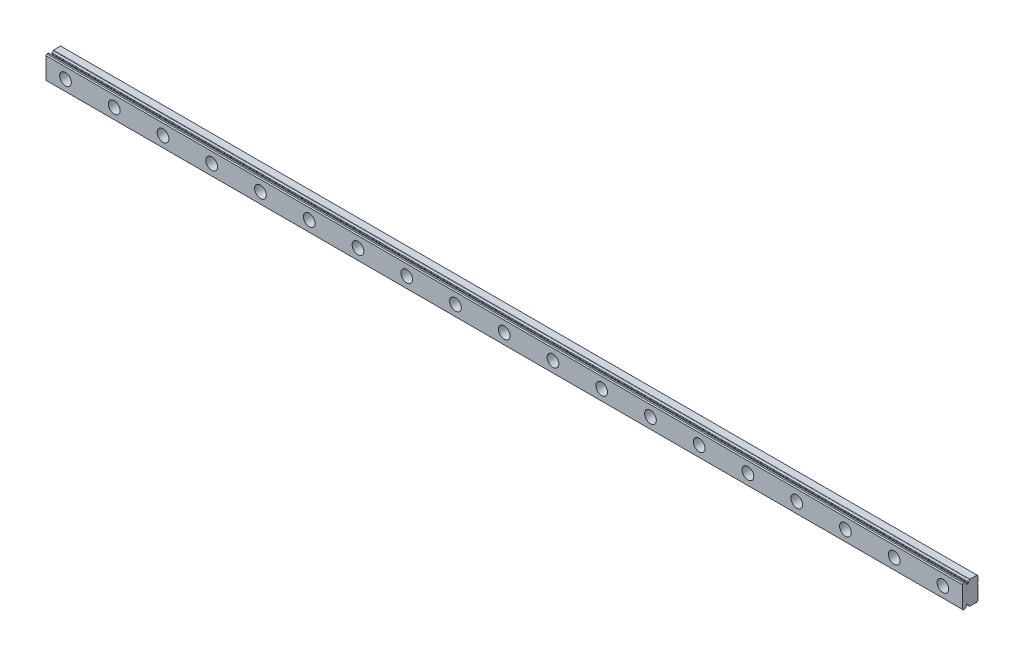
SolidWorks part; units mm, degrees
ref_plane "Front" through (0, 0, 0) normal (0, 0, 1) x (1, 0, 0)
ref_plane "Top" through (0, 0, 0) normal (0, 1, 0) x (1, 0, 0)
ref_plane "Right" through (0, 0, 0) normal (1, 0, 0) x (0, 0, -1)
ref_plane "Plane1" through (-10, 0, 0) normal (-1, 0, 0) x (0, -1, 0)
sketch "Sketch1" plane through (-10, 0, 0) normal (-1, 0, 0) x (0, -1, 0)
  line L0 (5.5, 0) -> (6, 0.5)
  line L1 (6, 0.5) -> (6, 4.1421)
  line L2 (5.0738, 4.9945) -> (4.7282, 5.0247)
  line L3 (4.5, 5.2738) -> (4.5, 5.7262)
  line L4 (4.7282, 5.9753) -> (5.0948, 6.0073)
  line L5 (6, 6.8254) -> (6, 7.5)
  line L6 (6, 7.5) -> (5.5, 8)
  line L7 (5.5, 8) -> (-5.5, 8)
  line L8 (-5.5, 8) -> (-6, 7.5)
  line L9 (-6, 7.5) -> (-6, 6.8254)
  line L10 (-5.0948, 6.0073) -> (-4.7282, 5.9753)
  line L11 (-4.5, 5.7262) -> (-4.5, 5.2738)
  line L12 (-4.7282, 5.0247) -> (-5.0738, 4.9945)
  line L13 (-6, 4.1421) -> (-6, 0.5)
  line L14 (-6, 0.5) -> (-5.5, 0)
  line L15 (-5.5, 0) -> (-2.4, 0)
  line L16 (-1.6, 0) -> (5.5, 0)
  arc A0 (6, 4.1421) -> (5.8448, 4.3734) centre (5.75, 4.1421) ccw
  arc A1 (5.8448, 4.3734) -> (5.2672, 4.8727) centre (6.3, 5.4838) cw
  arc A2 (5.2672, 4.8727) -> (5.0738, 4.9945) centre (5.052, 4.7455) ccw
  arc A3 (4.7282, 5.0247) -> (4.5, 5.2738) centre (4.75, 5.2738) cw
  arc A4 (4.5, 5.7262) -> (4.7282, 5.9753) centre (4.75, 5.7262) cw
  arc A5 (5.0948, 6.0073) -> (5.2845, 6.1232) centre (5.073, 6.2564) ccw
  arc A6 (5.2845, 6.1232) -> (5.8448, 6.5941) centre (6.3, 5.4838) cw
  arc A7 (5.8448, 6.5941) -> (6, 6.8254) centre (5.75, 6.8254) ccw
  arc A8 (-6, 6.8254) -> (-5.8448, 6.5941) centre (-5.75, 6.8254) ccw
  arc A9 (-5.8448, 6.5941) -> (-5.2845, 6.1232) centre (-6.3, 5.4838) cw
  arc A10 (-5.2845, 6.1232) -> (-5.0948, 6.0073) centre (-5.073, 6.2564) ccw
  arc A11 (-4.7282, 5.9753) -> (-4.5, 5.7262) centre (-4.75, 5.7262) cw
  arc A12 (-4.5, 5.2738) -> (-4.7282, 5.0247) centre (-4.75, 5.2738) cw
  arc A13 (-5.0738, 4.9945) -> (-5.2672, 4.8727) centre (-5.052, 4.7455) ccw
  arc A14 (-5.2672, 4.8727) -> (-5.8448, 4.3734) centre (-6.3, 5.4838) cw
  arc A15 (-5.8448, 4.3734) -> (-6, 4.1421) centre (-5.75, 4.1421) ccw
  arc A16 (-2.4, 0) -> (-1.6, 0) centre (-2, -0.3) cw
extrude "Boss-Extrude1" add sketch "Sketch1" against normal blind 470
hole_wizard "CBORE for M3 Hex Head Machine Screw2" positions "Sketch5" profile "Sketch4" counterbore size "M3" standard "ANSI Metric"
sketch "Sketch5" plane through (0, 0, 8) normal (0, 0, 1) x (1, 0, 0)
  point P0 (0, 0)
sketch "Sketch4" plane through (0, 0, 8) normal (1, 0, 0) x (0, -1, 0)
  line L0 (0, 0) -> (0, 8)
  line L1 (0, 8) -> (1.75, 8)
  line L3 (1.75, 8) -> (1.75, 4.5)
  line L4 (1.75, 4.5) -> (3, 4.5)
  line L5 (3, 4.5) -> (3, 0)
  line L7 (3, 0) -> (0, 0)
  line L11 (0, -6.35) -> (0, 107.95) construction
  dimension "Thru Hole Dia." = 3.5
  dimension "Thru Hole Depth" = 8
  dimension "C'Bore Dia." = 6
  dimension "C'Bore Depth" = 4.5
pattern_linear "LPattern2" count 19 spacing 25 along (1, 0, 0) of "CBORE for M3 Hex Head Machine Screw2"
